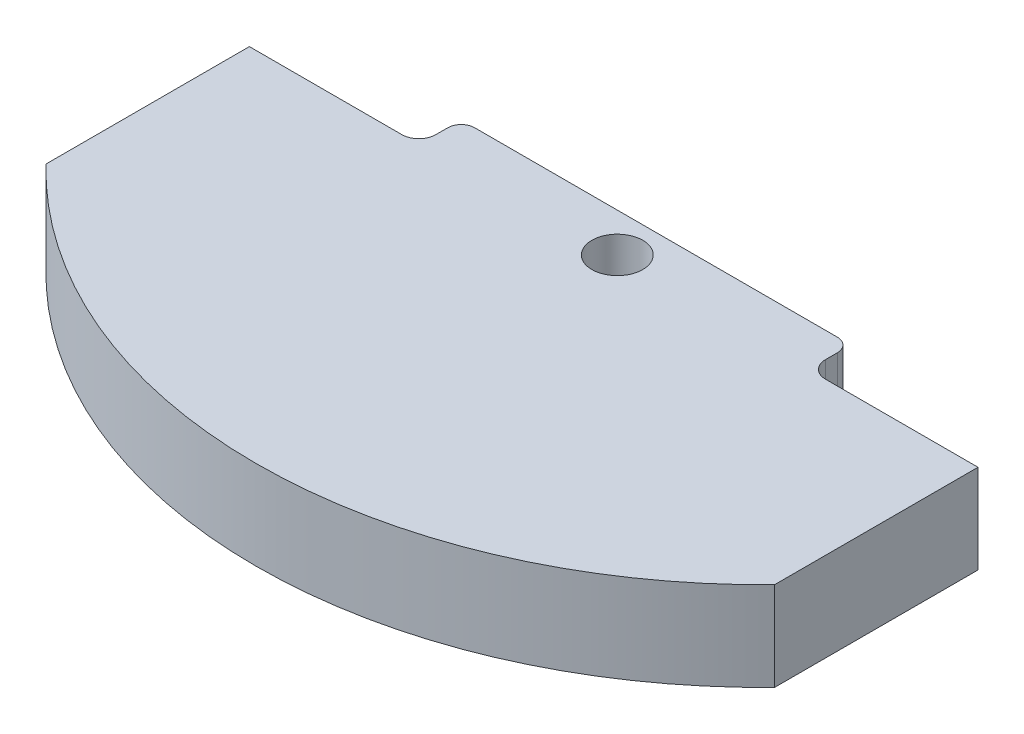
SolidWorks part; units mm, degrees
ref_plane "Front Plane" through (0, 0, 0) normal (0, 0, 1) x (1, 0, 0)
ref_plane "Top Plane" through (0, 0, 0) normal (0, 1, 0) x (1, 0, 0)
ref_plane "Right Plane" through (0, 0, 0) normal (1, 0, 0) x (0, 0, -1)
sketch "Sketch6" plane through (0, 0, 0) normal (0, 1, 0) x (1, 0, 0)
  line L1 (0, 0) -> (109.1946, 0)
  line L2 (0, 0) -> (0, -36.83)
  line L4 (109.1946, 0) -> (109.1946, -36.83)
  arc A0 (109.1946, -36.83) -> (0, -36.83) centre (54.5973, 16.039) cw
  dimension "D2" = 36.83
  dimension "D1" = 109.1946
extrude "Boss-Extrude2" add sketch "Sketch6" along normal blind 13.335
sketch "Sketch10" plane through (0, 13.335, 0) normal (0, 1, 0) x (1, 0, 0)
  line L0 (54.5973, 0) -> (54.5973, -59.961) construction
  line L1 (109.1946, 0) -> (0, 0) construction
  line L2 (109.1946, -6.35) -> (83.7946, -6.35)
  line L3 (0, 0) -> (25.4, 0)
  line L4 (0, 0) -> (0, -6.35)
  line L5 (0, -6.35) -> (25.4, -6.35)
  line L6 (25.4, 0) -> (25.4, -6.35)
  line L7 (83.7946, 0) -> (83.7946, -6.35)
  line L8 (109.1946, 0) -> (83.7946, 0)
  line L9 (109.1946, 0) -> (109.1946, -6.35)
  arc A0 (0, -36.83) -> (109.1946, -36.83) centre (54.5973, 16.039) ccw construction
  dimension "D1" = 25.4
  dimension "D2" = 6.35
extrude "Cut-Extrude1" cut sketch "Sketch10" against normal through all
fillet "Fillet1" radius 2.54 2 edges at (83.7946, 6.6675, 6.35) (25.4, 6.6675, 6.35)
fillet "Fillet2" radius 2.032 2 edges at (83.7946, 6.6675, 0) (25.4, 6.6675, 0)
sketch "Sketch11" plane through (0, 0, 0) normal (0, -1, 0) x (1, 0, 0)
  line L0 (25.4, 3.81) -> (25.4, 2.032) construction
  circle A3 centre (54.61, 5.8194) radius 3.81
  dimension "D1" = 29.21
extrude "Cut-Extrude2" cut sketch "Sketch11" against normal through all
